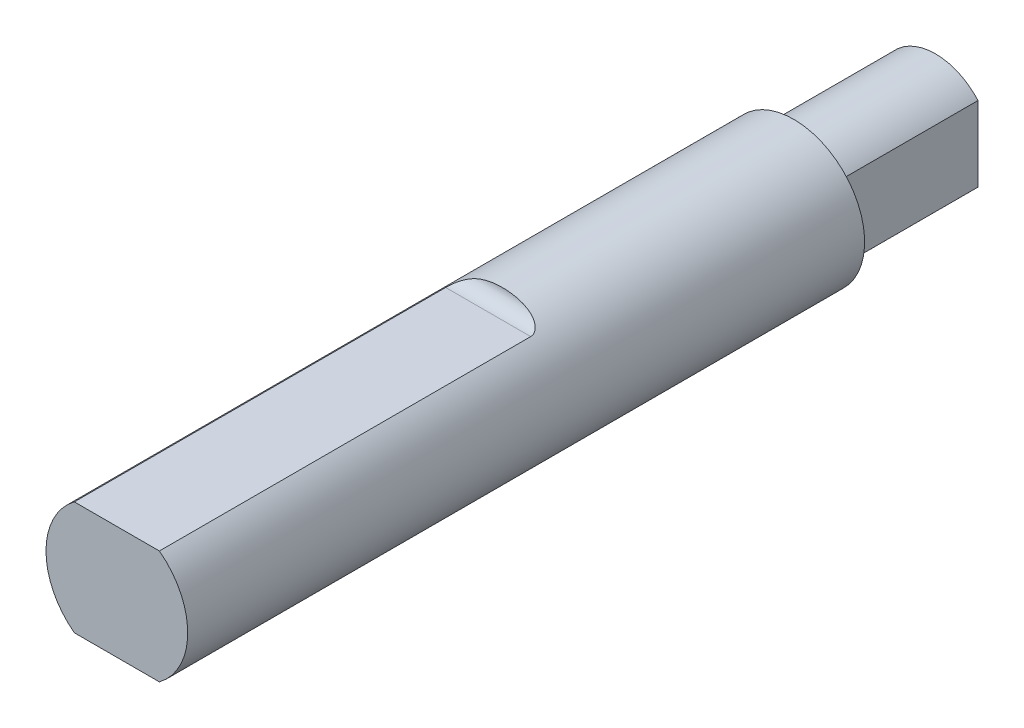
SolidWorks part; units mm, degrees
ref_plane "Front Plane" through (0, 0, 0) normal (0, 0, 1) x (1, 0, 0)
ref_plane "Top Plane" through (0, 0, 0) normal (0, 1, 0) x (1, 0, 0)
ref_plane "Right Plane" through (0, 0, 0) normal (1, 0, 0) x (0, 0, -1)
sketch "Sketch1" plane through (0, 0, 0) normal (0, 0, 1) x (1, 0, 0)
  circle A0 centre (0, 0) radius 2.5
  dimension "D1" = 5
extrude "Boss-Extrude1" add sketch "Sketch1" along normal blind 28.879
sketch "Sketch2" plane through (0, 0, 0) normal (0, 0, -1) x (-1, 0, 0)
  line L0 (-1.5, 1.3229) -> (-1.5, -1.3229)
  line L1 (1.5, -1.3229) -> (1.5, 1.3229)
  arc A1 (-1.5, -1.3229) -> (1.5, -1.3229) centre (0, 0) ccw
  arc A3 (-1.5, 1.3229) -> (1.5, 1.3229) centre (0, 0) cw
  circle A5 centre (0, 0) radius 2.5
  circle A6 centre (0, 0) radius 2.5
  dimension "D2" = 4
  dimension "D1" = 3
  dimension "D3" = 0
extrude "Cut-Extrude1" cut sketch "Sketch2" against normal blind 5
sketch "Sketch3" plane through (0, 0, 28.879) normal (0, 0, 1) x (1, 0, 0)
  line L0 (-1.5, 2) -> (1.5, 2)
  line L1 (-2.5, 0) -> (2.5, 0) construction
  line L2 (-1.5, -2) -> (1.5, -2)
  circle A0 centre (0, 0) radius 2.5 construction
  arc A1 (1.5, 2) -> (-1.5, 2) centre (0, 0) ccw
  arc A2 (1.5, -2) -> (-1.5, -2) centre (0, 0) cw
  dimension "D1" = 4
extrude "Cut-Extrude2" cut sketch "Sketch3" against normal blind 13.1
sketch "Sketch4" plane through (0, 0, 0) normal (1, 0, 0) x (0, 0, -1)
  line L0 (-15.779, 2.5) -> (-15.779, 2)
  line L1 (-15.279, 2.5) -> (-15.779, 2.5)
  line L2 (-15.779, -2.5) -> (-15.779, -2)
  line L3 (-15.779, -2) -> (-15.779, -2.5) construction
  line L4 (-15.779, -2.5) -> (-5, -2.5) construction
  line L5 (-15.279, -2.5) -> (-15.779, -2.5)
  line L6 (-5, 2.5) -> (-15.779, 2.5) construction
  arc A0 (-15.779, 2) -> (-15.279, 2.5) centre (-15.779, 2.5) ccw
  arc A1 (-15.779, -2) -> (-15.279, -2.5) centre (-15.779, -2.5) cw
extrude "Cut-Extrude3" cut sketch "Sketch4" against normal through all both and the other way through all
